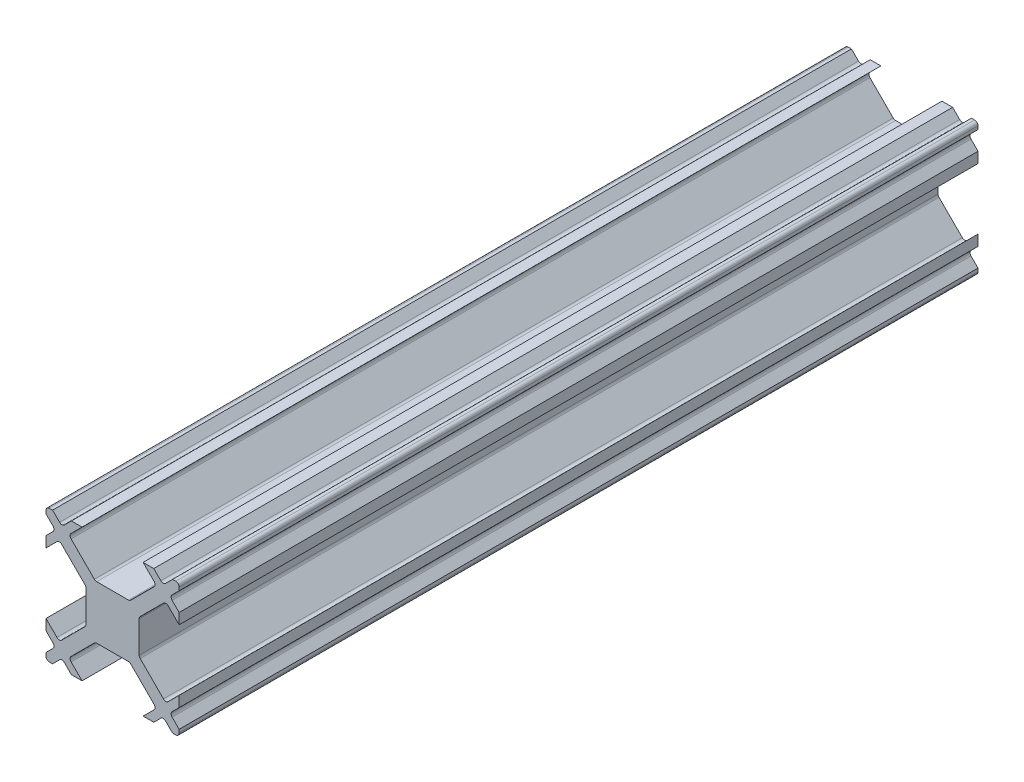
SolidWorks part; units mm, degrees
material "6063-T6"
ref_plane "Front Plane" through (0, 0, 0) normal (0, 0, 1) x (1, 0, 0)
ref_plane "Top Plane" through (0, 0, 0) normal (0, 1, 0) x (1, 0, 0)
ref_plane "Right Plane" through (0, 0, 0) normal (1, 0, 0) x (0, 0, -1)
ref_plane "Plane1" through (0, 0, 12.5) normal (0, 0, 1) x (1, 0, 0)
sketch "Sketch1" plane through (0, 0, 12.5) normal (0, 0, 1) x (1, 0, 0)
  line L0 (1.1893, 2) -> (-1.1893, 2)
  line L1 (-1.3661, 2.0732) -> (-3.1161, 3.8232)
  line L2 (-3.1161, 4.1768) -> (-2.2929, 5)
  line L3 (-2.2929, 5) -> (-3.095, 5)
  line L4 (-3.095, 5) -> (-3.6232, 4.4718)
  line L5 (-3.9768, 4.4718) -> (-4.505, 5)
  line L6 (-4.505, 5) -> (-4.75, 5)
  line L7 (-5, 4.75) -> (-5, 4.505)
  line L8 (-5, 4.505) -> (-4.4718, 3.9768)
  line L9 (-4.4718, 3.6232) -> (-5, 3.095)
  line L10 (-5, 3.095) -> (-5, 2.2929)
  line L11 (-5, 2.2929) -> (-4.1768, 3.1161)
  line L12 (-3.8232, 3.1161) -> (-2.0732, 1.3661)
  line L13 (-2, 1.1893) -> (-2, -1.1893)
  line L14 (-2.0732, -1.3661) -> (-3.8232, -3.1161)
  line L15 (-4.1768, -3.1161) -> (-5, -2.2929)
  line L16 (-5, -2.2929) -> (-5, -3.095)
  line L17 (-5, -3.095) -> (-4.4718, -3.6232)
  line L18 (-4.4718, -3.9768) -> (-5, -4.505)
  line L19 (-5, -4.505) -> (-5, -4.75)
  line L20 (-4.75, -5) -> (-4.505, -5)
  line L21 (-4.505, -5) -> (-3.9768, -4.4718)
  line L22 (-3.6232, -4.4718) -> (-3.095, -5)
  line L23 (-3.095, -5) -> (-2.2929, -5)
  line L24 (-2.2929, -5) -> (-3.1161, -4.1768)
  line L25 (-3.1161, -3.8232) -> (-1.3661, -2.0732)
  line L26 (-1.1893, -2) -> (1.1893, -2)
  line L27 (1.3661, -2.0732) -> (3.1161, -3.8232)
  line L28 (3.1161, -4.1768) -> (2.2929, -5)
  line L29 (2.2929, -5) -> (3.095, -5)
  line L30 (3.095, -5) -> (3.6232, -4.4718)
  line L31 (3.9768, -4.4718) -> (4.505, -5)
  line L32 (4.505, -5) -> (4.75, -5)
  line L33 (5, -4.75) -> (5, -4.505)
  line L34 (5, -4.505) -> (4.4718, -3.9768)
  line L35 (4.4718, -3.6232) -> (5, -3.095)
  line L36 (5, -3.095) -> (5, -2.2929)
  line L37 (5, -2.2929) -> (4.1768, -3.1161)
  line L38 (3.8232, -3.1161) -> (2.0732, -1.3661)
  line L39 (2, -1.1893) -> (2, 1.1893)
  line L40 (2.0732, 1.3661) -> (3.8232, 3.1161)
  line L41 (4.1768, 3.1161) -> (5, 2.2929)
  line L42 (5, 2.2929) -> (5, 3.095)
  line L43 (5, 3.095) -> (4.4718, 3.6232)
  line L44 (4.4718, 3.9768) -> (5, 4.505)
  line L45 (5, 4.505) -> (5, 4.75)
  line L46 (4.75, 5) -> (4.505, 5)
  line L47 (4.505, 5) -> (3.9768, 4.4718)
  line L48 (3.6232, 4.4718) -> (3.095, 5)
  line L49 (3.095, 5) -> (2.2929, 5)
  line L50 (2.2929, 5) -> (3.1161, 4.1768)
  line L51 (3.1161, 3.8232) -> (1.3661, 2.0732)
  arc A0 (1.3661, 2.0732) -> (1.1893, 2) centre (1.1893, 2.25) cw
  arc A1 (-1.1893, 2) -> (-1.3661, 2.0732) centre (-1.1893, 2.25) cw
  arc A2 (-3.1161, 3.8232) -> (-3.1161, 4.1768) centre (-2.9393, 4) cw
  arc A3 (-3.6232, 4.4718) -> (-3.9768, 4.4718) centre (-3.8, 4.6485) cw
  arc A4 (-4.75, 5) -> (-5, 4.75) centre (-4.75, 4.75) ccw
  arc A5 (-4.4718, 3.9768) -> (-4.4718, 3.6232) centre (-4.6485, 3.8) cw
  arc A6 (-4.1768, 3.1161) -> (-3.8232, 3.1161) centre (-4, 2.9393) cw
  arc A7 (-2.0732, 1.3661) -> (-2, 1.1893) centre (-2.25, 1.1893) cw
  arc A8 (-2, -1.1893) -> (-2.0732, -1.3661) centre (-2.25, -1.1893) cw
  arc A9 (-3.8232, -3.1161) -> (-4.1768, -3.1161) centre (-4, -2.9393) cw
  arc A10 (-4.4718, -3.6232) -> (-4.4718, -3.9768) centre (-4.6485, -3.8) cw
  arc A11 (-5, -4.75) -> (-4.75, -5) centre (-4.75, -4.75) ccw
  arc A12 (-3.9768, -4.4718) -> (-3.6232, -4.4718) centre (-3.8, -4.6485) cw
  arc A13 (-3.1161, -4.1768) -> (-3.1161, -3.8232) centre (-2.9393, -4) cw
  arc A14 (-1.3661, -2.0732) -> (-1.1893, -2) centre (-1.1893, -2.25) cw
  arc A15 (1.1893, -2) -> (1.3661, -2.0732) centre (1.1893, -2.25) cw
  arc A16 (3.1161, -3.8232) -> (3.1161, -4.1768) centre (2.9393, -4) cw
  arc A17 (3.6232, -4.4718) -> (3.9768, -4.4718) centre (3.8, -4.6485) cw
  arc A18 (4.75, -5) -> (5, -4.75) centre (4.75, -4.75) ccw
  arc A19 (4.4718, -3.9768) -> (4.4718, -3.6232) centre (4.6485, -3.8) cw
  arc A20 (4.1768, -3.1161) -> (3.8232, -3.1161) centre (4, -2.9393) cw
  arc A21 (2.0732, -1.3661) -> (2, -1.1893) centre (2.25, -1.1893) cw
  arc A22 (2, 1.1893) -> (2.0732, 1.3661) centre (2.25, 1.1893) cw
  arc A23 (3.8232, 3.1161) -> (4.1768, 3.1161) centre (4, 2.9393) cw
  arc A24 (4.4718, 3.6232) -> (4.4718, 3.9768) centre (4.6485, 3.8) cw
  arc A25 (5, 4.75) -> (4.75, 5) centre (4.75, 4.75) ccw
  arc A26 (3.9768, 4.4718) -> (3.6232, 4.4718) centre (3.8, 4.6485) cw
  arc A27 (3.1161, 4.1768) -> (3.1161, 3.8232) centre (2.9393, 4) cw
extrude "Boss-Extrude1" add sketch "Sketch1" against normal blind 60
